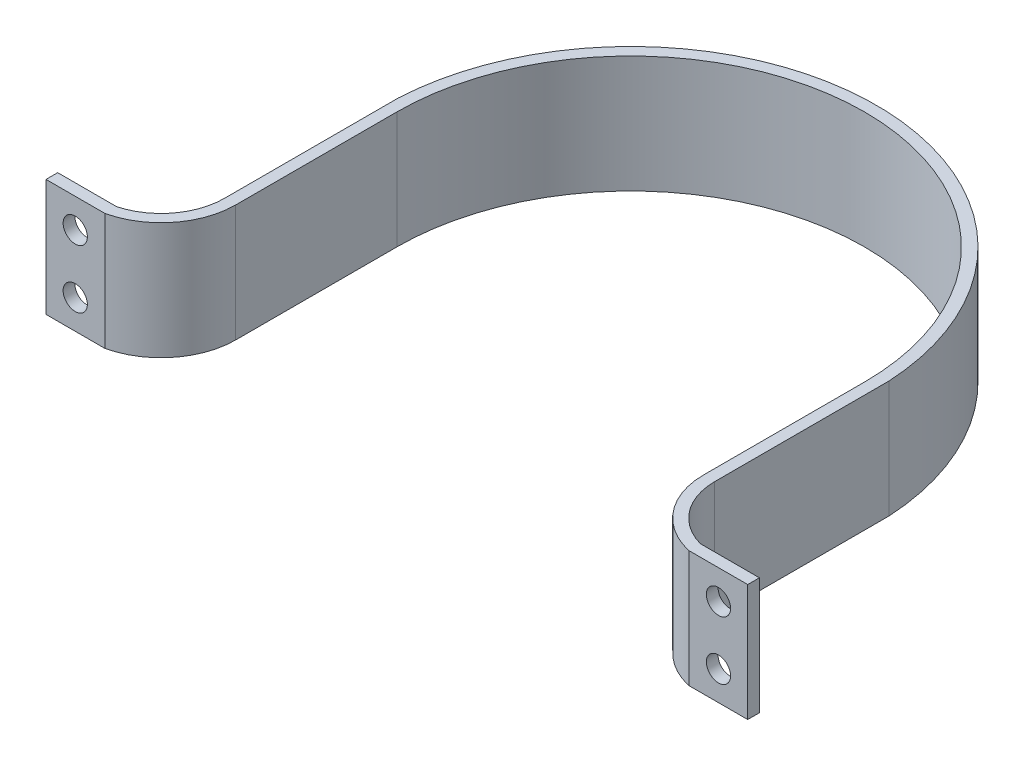
SolidWorks part; units mm, degrees
material "1023 Tôle d'acier au carbone (SS)"
ref_plane "Plan de face" through (0, 0, 0) normal (0, 0, 1) x (1, 0, 0)
ref_plane "Plan de dessus" through (0, 0, 0) normal (0, 1, 0) x (1, 0, 0)
ref_plane "Plan de droite" through (0, 0, 0) normal (1, 0, 0) x (0, 0, -1)
sketch "Esquisse2" plane through (0, 0, 0) normal (0, 1, 0) x (1, 0, 0)
  line L0 (0, 0) -> (0, 5.5733)
  line L1 (24.9635, -20) -> (30.0035, -20)
  line L2 (-30.0035, -20) -> (-30.0035, -19)
  line L3 (24.9635, -19) -> (30.0035, -19)
  line L4 (30.0035, -20) -> (30.0035, -19)
  line L5 (-30.0035, -20) -> (-30.0035, -19)
  line L6 (-24.9635, -20) -> (-30.0035, -20)
  line L7 (20.9702, -13.8024) -> (20.9702, 1.1186)
  line L8 (-24.9635, -19) -> (-30.0035, -19)
  line L9 (20, -13.8024) -> (20, 0)
  line L10 (-20, -13.8024) -> (-20, 0)
  line L11 (-20.9702, -13.8024) -> (-20.9702, 1.1186)
  arc A0 (20, 0) -> (-20, 0) centre (0, 0) ccw
  circle A1 centre (0, 0) radius 20 construction
  arc A2 (20.9702, 1.1186) -> (-20.9702, 1.1186) centre (0, 0) ccw
  arc A3 (20.9702, -13.8024) -> (24.9635, -19) centre (26.3897, -13.7714) ccw
  arc A4 (20, -13.8024) -> (24.9635, -20) centre (26.3897, -13.7714) ccw
  arc A5 (-20.9702, -13.8024) -> (-24.9635, -19) centre (-26.3897, -13.7714) cw
  arc A6 (-20, -13.8024) -> (-24.9635, -20) centre (-26.3897, -13.7714) cw
  point P16 (24.9635, -20.3839)
  point P20 (0, 0)
  point P21 (0, 0)
  point P22 (0, 0)
  point P23 (0, 0)
  point P24 (0, 0)
  point P25 (0, 0)
  point P26 (0, 0)
  point P27 (0, 0)
  point P28 (0, 0)
  point P29 (0, 0)
  point P30 (0, 0)
  point P31 (0, 0)
  dimension "D1" = 20
  dimension "D3" = 21
  dimension "D2" = 20
  dimension "D4" = 1
  dimension "D5" = 5.04
  dimension "D6" = 5.04
extrude "Boss.-Extru.1" add sketch "Esquisse2" along normal blind 10 contours L6 A6 L10 A0 L9 A4 L1 L4 L3 A3 L7 A2 L11 A5 L8 L5
sketch "Esquisse5" plane through (0, 0, 20) normal (0, 0, 1) x (1, 0, 0)
  line L0 (-30.0035, 10) -> (-30.0035, 0) construction
  line L1 (-24.9635, 10) -> (-30.0035, 10) construction
  line L2 (-30.0035, 5) -> (-27.4635, 5)
  line L3 (0, 0) -> (0, 4.2463)
  circle A0 centre (-27.5035, 7.5) radius 1.0361
  circle A1 centre (-27.5035, 2.5) radius 1.0361
  circle A2 centre (27.5035, 2.5) radius 1.0361
  circle A3 centre (27.5035, 7.5) radius 1.0361
  dimension "D1" = 2.5
  dimension "D2" = 2.5
extrude "Enlèv. mat.-Extru.2" cut sketch "Esquisse5" against normal through all contours A0 | A1 | A2 | A3
